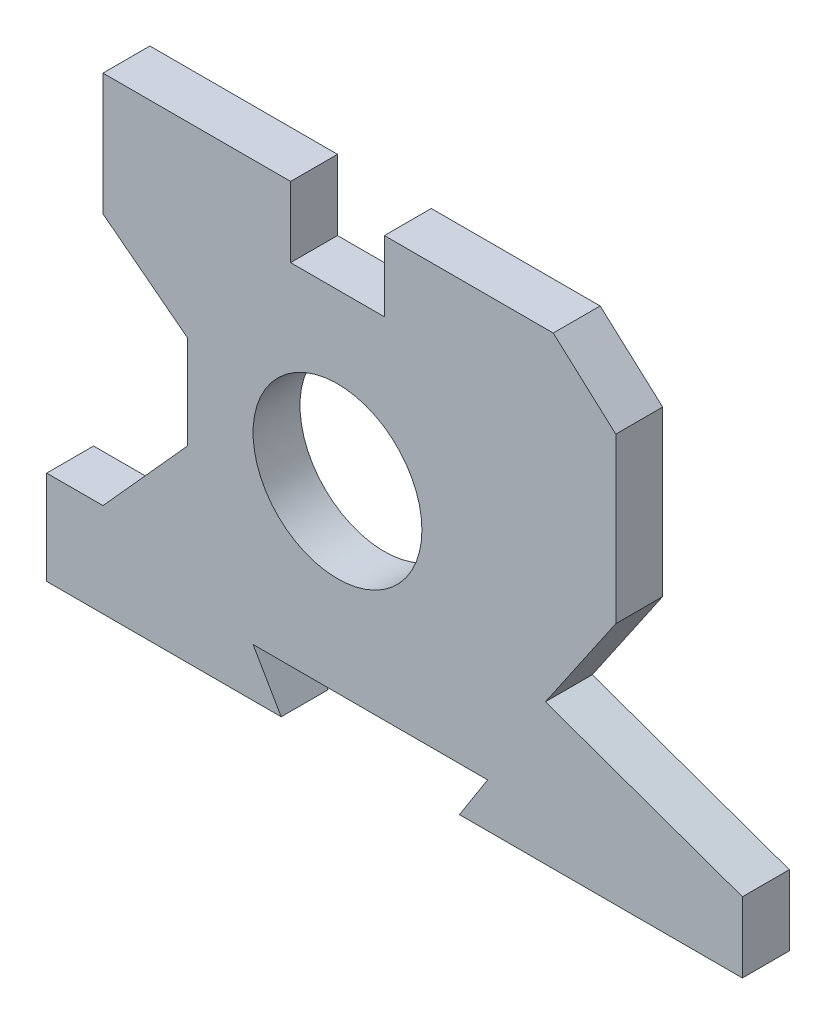
SolidWorks part; units mm, degrees
ref_plane "Front Plane" through (0, 0, 0) normal (0, 0, 1) x (1, 0, 0)
ref_plane "Top Plane" through (0, 0, 0) normal (0, 1, 0) x (1, 0, 0)
ref_plane "Right Plane" through (0, 0, 0) normal (1, 0, 0) x (0, 0, -1)
sketch "Sketch1" plane through (0, 0, 0) normal (0, 0, 1) x (1, 0, 0)
  line L0 (17.4233, -47.2254) -> (77.7533, -47.2254)
  line L1 (-58.5767, 51.6946) -> (-18.5767, 51.6946)
  line L3 (-70.5767, -48.1652) -> (-20.5767, -48.1652)
  line L4 (77.7533, -32.2254) -> (77.7533, -47.2254)
  line L10 (-58.5767, 51.6946) -> (-58.5767, 25.6946)
  line L11 (-40.5767, -8.1652) -> (-40.5767, 11.8348)
  line L12 (-40.5767, 11.8348) -> (-58.5767, 25.6946)
  line L16 (-58.5767, -28.1652) -> (-40.5767, -8.1652)
  line L18 (1.4233, 51.6946) -> (1.4233, 36.6946)
  line L19 (1.4233, 36.6946) -> (-18.5767, 36.6946)
  line L20 (-18.5767, 51.6946) -> (-18.5767, 36.6946)
  line L21 (-70.5767, -28.1652) -> (-70.5767, -48.1652)
  line L22 (-58.5767, -28.1652) -> (-70.5767, -28.1652)
  line L23 (-20.5767, -48.1652) -> (-26.5767, -37.8054)
  line L24 (-26.5767, -37.8054) -> (23.4233, -37.8054)
  line L25 (23.4233, -37.8054) -> (17.4233, -47.2254)
  line L26 (77.7533, -32.2254) -> (35.7533, -17.2254)
  line L27 (35.7533, -17.2254) -> (50.7533, 4.6946)
  line L28 (50.7533, 4.6946) -> (50.7533, 39.6946)
  line L29 (50.7533, 39.6946) -> (37.4233, 51.6946)
  line L30 (1.4233, 51.6946) -> (37.4233, 51.6946)
  circle A0 centre (-8.5767, 1.3348) radius 18
  point P0 (-8.5767, 1.3348)
  point P10 (0, 49.46)
  dimension "D25" = 36
  dimension "D1" = 40
  dimension "D2" = 20
  dimension "D3" = 50
  dimension "D4" = 109.33
  dimension "D5" = 13.33
  dimension "D6" = 26
  dimension "D7" = 12
  dimension "D8" = 15
  dimension "D9" = 47
  dimension "D10" = 20
  dimension "D11" = 20
  dimension "D12" = 49.5
  dimension "D13" = 12
  dimension "D14" = 50
  dimension "D15" = 6
  dimension "D16" = 6
  dimension "D17" = 42
  dimension "D18" = 15
  dimension "D19" = 30
  dimension "D20" = 20
  dimension "98.92" = 98.92
  dimension "D21" = 30
  dimension "D22" = 50
  dimension "D23" = 9.42
  dimension "D24" = 148.33
extrude "Boss-Extrude2" add sketch "Sketch1" along normal blind 10 contours L26 L27 L28 L29 L30 L18 L19 L20 L1 L10 L12 L11 L16 L22 L21 L3 L23 L24 L25 L0 L4 | A0
